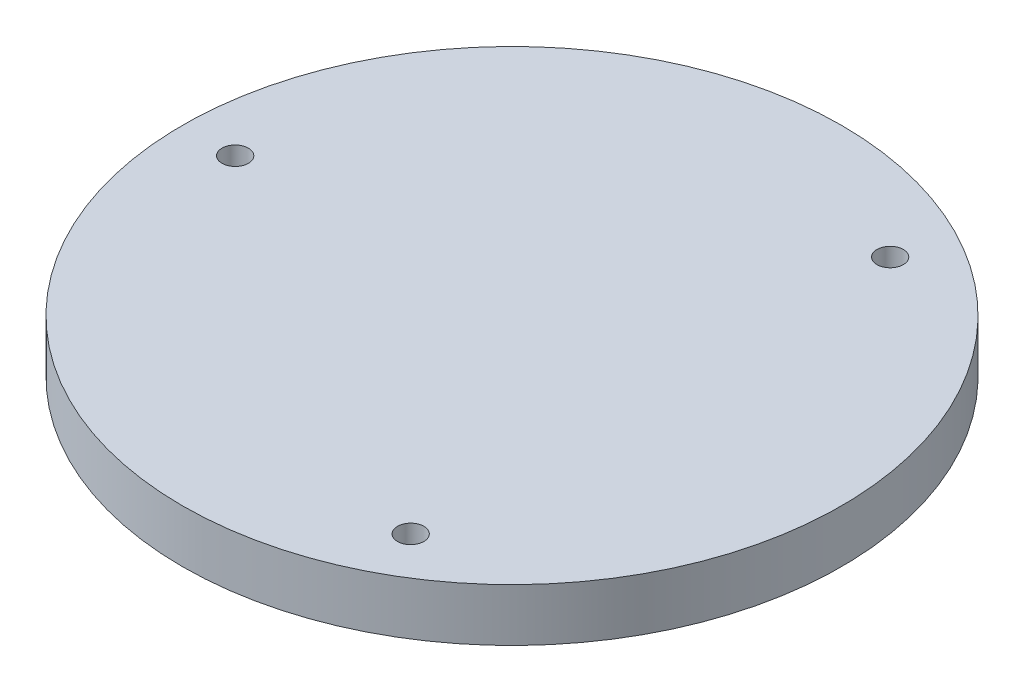
SolidWorks part; units mm, degrees
material "AISI 316 Stainless Steel Sheet (SS)"
ref_plane "Front Plane" through (0, 0, 0) normal (0, 0, 1) x (1, 0, 0)
ref_plane "Top Plane" through (0, 0, 0) normal (0, 1, 0) x (1, 0, 0)
ref_plane "Right Plane" through (0, 0, 0) normal (1, 0, 0) x (0, 0, -1)
sketch "Sketch1" plane through (0, 0, 0) normal (0, 1, 0) x (1, 0, 0)
  circle A0 centre (0, 0) radius 125
  dimension "D1" = 250
extrude "Plate" add sketch "Sketch1" along normal blind 20
hole_wizard "CBORE for M5 Hex Socket Head Cap Screw1" positions "Sketch2" profile "Sketch3" counterbore size "M5" standard "ISO" end condition through all
sketch "Sketch2" plane through (0, 20, 0) normal (0, 1, 0) x (1, 0, 0)
  line L0 (-105, 0) -> (0, 0) construction
  point P0 (-105, 0)
  dimension "D1" = 105
sketch "Sketch3" plane through (-105, 20, 0) normal (1, 0, 0) x (0, 0, 1)
  line L0 (0, 0) -> (0, 20)
  line L1 (0, 20) -> (2.65, 20)
  line L3 (2.65, 20) -> (2.65, 15.4)
  line L4 (2.65, 15.4) -> (5, 15.4)
  line L5 (5, 15.4) -> (5, 0)
  line L7 (5, 0) -> (0, 0)
  line L11 (0, -6.35) -> (0, 107.95) construction
  dimension "Thru Hole Dia." = 5.3
  dimension "Thru Hole Depth" = 20
  dimension "C'Bore Dia." = 10
  dimension "C'Bore Depth" = 15.4
pattern_circular "CirPattern1" count 3 over 360 about axis through (0, 0, 0) along (0, 1, 0) of "CBORE for M5 Hex Socket Head Cap Screw1"
